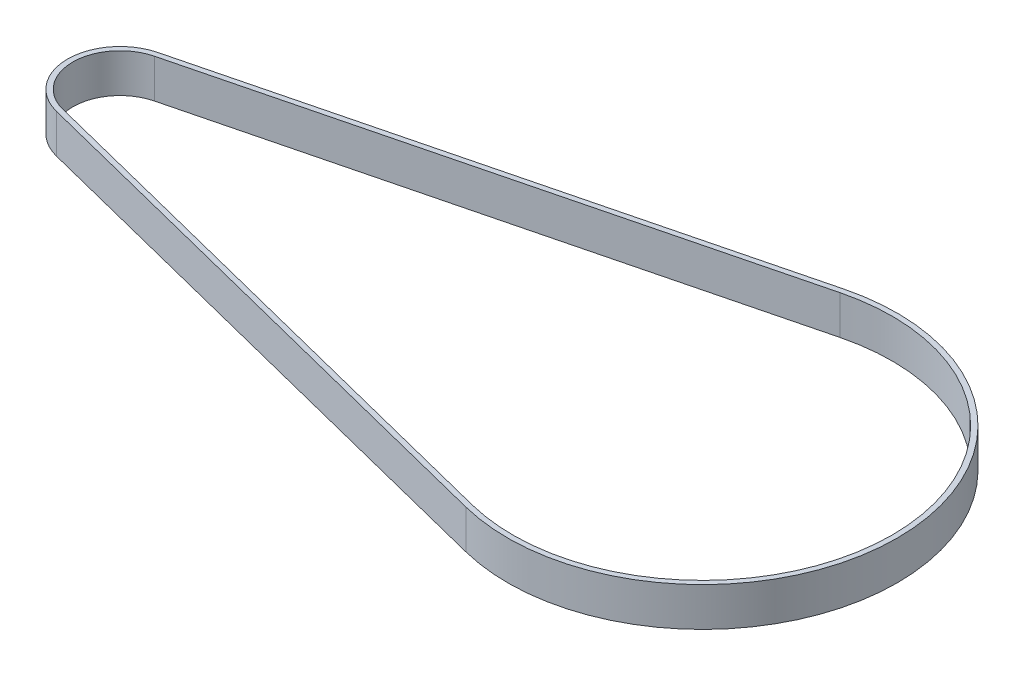
SolidWorks part; units mm, degrees
ref_plane "Front Plane" through (0, 0, 0) normal (0, 0, 1) x (1, 0, 0)
ref_plane "Top Plane" through (0, 0, 0) normal (0, 1, 0) x (1, 0, 0)
ref_plane "Right Plane" through (0, 0, 0) normal (1, 0, 0) x (0, 0, -1)
sketch "Sketch1" plane through (0, 0, 0) normal (0, 1, 0) x (1, 0, 0)
  line L0 (-91.7844, 7.0785) -> (-7.1622, 28.4111)
  line L1 (-91.7844, -7.0785) -> (-7.1622, -28.4111)
  line L2 (-91.98, 7.8543) -> (-7.3578, 29.1869)
  line L3 (-91.98, -7.8543) -> (-7.3578, -29.1869)
  arc A0 (-7.1622, -28.4111) -> (-7.1622, 28.4111) centre (0, 0) ccw
  arc A1 (-91.7844, 7.0785) -> (-91.7844, -7.0785) centre (-90, 0) ccw
  arc A2 (-7.3578, -29.1869) -> (-7.3578, 29.1869) centre (0, 0) ccw
  arc A3 (-91.98, 7.8543) -> (-91.98, -7.8543) centre (-90, 0) ccw
  dimension "D1" = 14.6
  dimension "D2" = 58.6
  dimension "D3" = 90
  dimension "D4" = 0.8
extrude "Boss-Extrude1" add sketch "Sketch1" along normal blind 6
